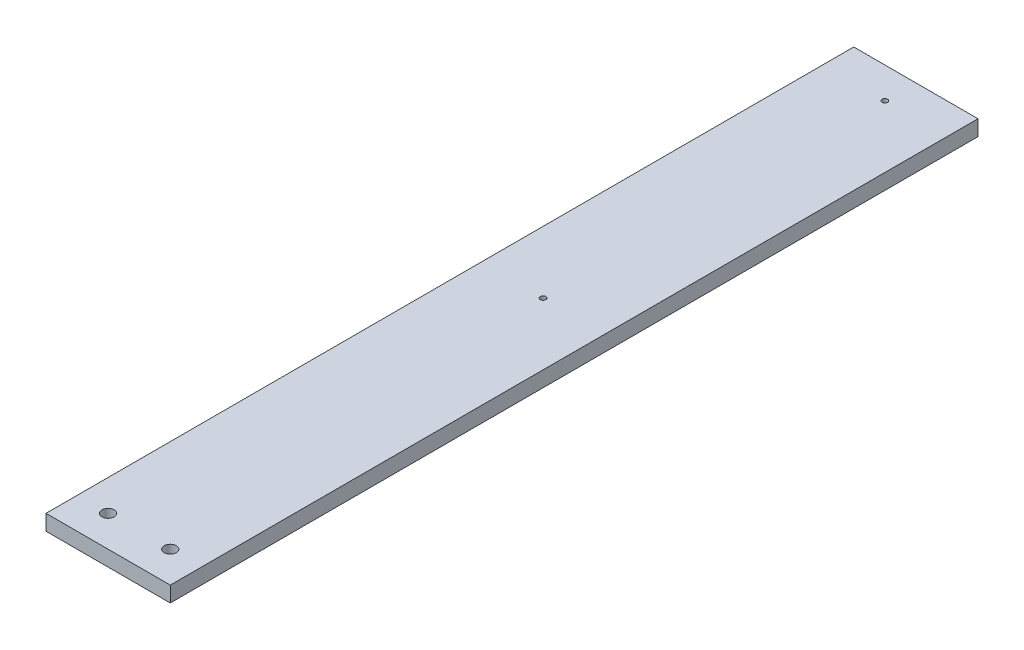
SolidWorks part; units mm, degrees
material "6061-T6 (SS)"
ref_plane "Front Plane" through (0, 0, 0) normal (0, 0, 1) x (1, 0, 0)
ref_plane "Top Plane" through (0, 0, 0) normal (0, 1, 0) x (1, 0, 0)
ref_plane "Right Plane" through (0, 0, 0) normal (1, 0, 0) x (0, 0, -1)
sketch "Sketch1" plane through (0, 0, 0) normal (0, 0, 1) x (1, 0, 0)
  line L0 (0, 0) -> (50.8, 0)
  dimension "D1" = 50.8
extrude "Extrude-Thin1" add sketch "Sketch1" along normal blind 330.2 thin
sketch "Sketch3" plane through (0, 0, 0) normal (0, 1, 0) x (1, 0, 0)
  line L0 (0, -317.5) -> (50.8, -317.5) construction
  line L1 (0, -330.2) -> (0, 0) construction
  line L2 (50.8, -330.2) -> (50.8, 0) construction
  line L3 (0, -330.2) -> (50.8, -330.2) construction
  circle A0 centre (12.7, -317.5) radius 2.4892
  circle A1 centre (38.1, -317.5) radius 2.4892
  dimension "D2" = 4.9784
  dimension "D3" = 12.7
  dimension "D4" = 25.4
  dimension "D1" = 12.7
extrude "Cut-Extrude1" cut sketch "Sketch3" against normal through all
sketch "Sketch4" plane through (0, 0, 0) normal (0, 1, 0) x (1, 0, 0)
  line L0 (25.4, 0) -> (25.4, -12.7) construction
  line L1 (0, 0) -> (50.8, 0) construction
  line L2 (25.4, -12.7) -> (25.4, -152.4) construction
  dimension "D1" = 12.7
  dimension "D2" = 139.7
hole_wizard "#4-40 Tapped Hole1" positions "Sketch5" profile "Sketch6" tap size "#4-40" standard "ANSI Inch"
sketch "Sketch5" plane through (0, 0, 0) normal (0, 1, 0) x (1, 0, 0)
  point P0 (25.4, -152.4)
  point P3 (25.4, -12.7)
sketch "Sketch6" plane through (25.4, 0, 152.4) normal (1, 0, 0) x (0, 0, 1)
  line L0 (0, 0) -> (0, 8.2992)
  line L1 (0, 8.2992) -> (1.1303, 7.62)
  line L2 (1.1303, 7.62) -> (1.1303, 0)
  line L5 (1.1303, 0) -> (0, 0)
  line L10 (0, 8.2992) -> (-1.1303, 7.62) construction
  line L11 (0, -6.35) -> (0, 107.95) construction
  dimension "Tap Drill Dia." = 2.2606
  dimension "Tap Drill Depth" = 7.62
  dimension "Drill Angle" = 118
cosmetic thread "Hole Thread1" parameters "D1"=5.588, "D2"=2.8448
cosmetic thread "Hole Thread2" parameters "D1"=5.588, "D2"=2.8448
equation "\"Thick\"= \"in\""
equation "\"Magnet Dist\"= 5.5in"
equation "\"D2@Sketch4\"=\"Magnet Dist\""
